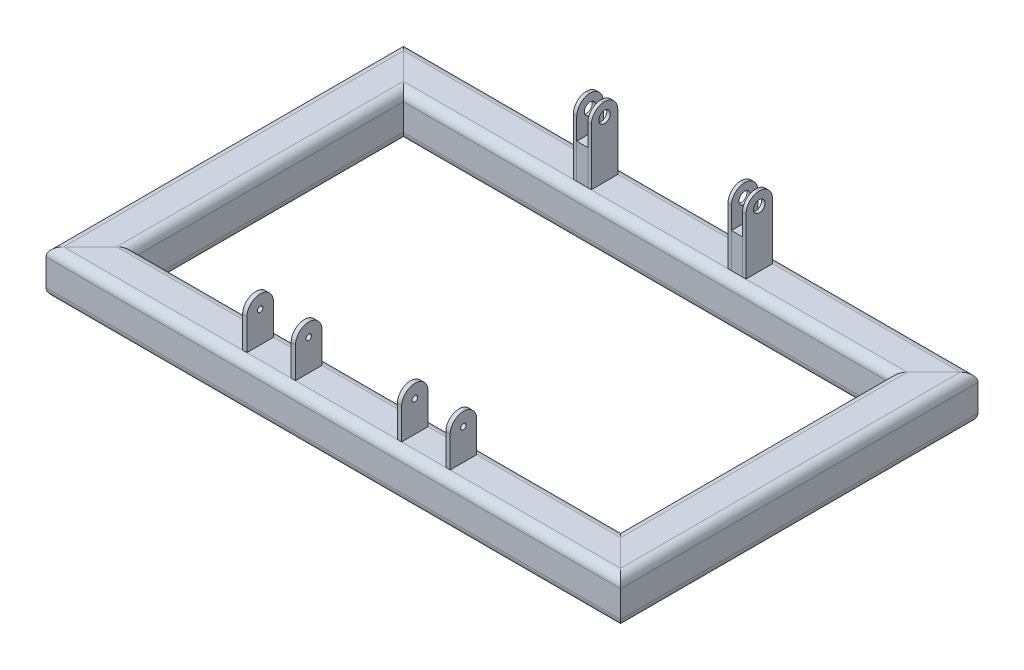
SolidWorks part; units mm, degrees
ref_plane "Front Plane" through (0, 0, 0) normal (0, 0, 1) x (1, 0, 0)
ref_plane "Top Plane" through (0, 0, 0) normal (0, 1, 0) x (1, 0, 0)
ref_plane "Right Plane" through (0, 0, 0) normal (1, 0, 0) x (0, 0, -1)
sketch "Sketch1" plane through (0, 0, 0) normal (0, 1, 0) x (1, 0, 0)
  line L0 (0, 0) -> (0, 180)
  line L5 (0, 180) -> (304.8, 180)
  line L6 (304.8, 180) -> (304.8, 0)
  line L7 (304.8, 0) -> (0, 0)
  dimension "D1" = 180
  dimension "D2" = 304.8
other "Tube square TS25X25X2.5(1)"
ref_plane "Plane1" through (304.8, 0, 0) normal (-1, 0, 0) x (0, 0, 1)
sketch "Sketch123" plane through (304.8, 0, 0) normal (-1, 0, 0) x (0, 0, 1)
  line L0 (-7.62, -10.16) -> (7.62, -10.16)
  line L1 (-10.16, -7.62) -> (-10.16, 7.62)
  line L2 (7.62, 10.16) -> (-7.62, 10.16)
  line L3 (10.16, 7.62) -> (10.16, -7.62)
  line L4 (-7.62, -12.7) -> (7.62, -12.7)
  line L5 (-12.7, -7.62) -> (-12.7, 7.62)
  line L6 (7.62, 12.7) -> (-7.62, 12.7)
  line L7 (12.7, 7.62) -> (12.7, -7.62)
  line L8 (-12.7, 0) -> (-10.16, 0) construction
  line L9 (-10.16, 0) -> (10.16, 0) construction
  line L10 (10.16, 0) -> (12.7, 0) construction
  line L11 (0, 12.7) -> (0, 10.16) construction
  line L12 (0, 10.16) -> (0, -10.16) construction
  line L13 (0, -10.16) -> (0, -12.7) construction
  arc A0 (12.7, 7.62) -> (7.62, 12.7) centre (7.62, 7.62) ccw
  arc A1 (7.62, -12.7) -> (12.7, -7.62) centre (7.62, -7.62) ccw
  arc A2 (-12.7, -7.62) -> (-7.62, -12.7) centre (-7.62, -7.62) ccw
  arc A3 (-7.62, 12.7) -> (-12.7, 7.62) centre (-7.62, 7.62) ccw
  arc A4 (-7.62, 10.16) -> (-10.16, 7.62) centre (-7.62, 7.62) ccw
  arc A5 (10.16, 7.62) -> (7.62, 10.16) centre (7.62, 7.62) ccw
  arc A6 (7.62, -10.16) -> (10.16, -7.62) centre (7.62, -7.62) ccw
  arc A7 (-10.16, -7.62) -> (-7.62, -10.16) centre (-7.62, -7.62) ccw
  point P6 (-12.7, 12.7)
  point P33 (12.7, 12.7)
  point P34 (-12.7, -12.7)
  point P36 (12.7, -12.7)
  point P37 (0, 0)
  point P38 (0, 0)
  dimension "D1" = 5.08
  dimension "Thickness" = 2.54
  dimension "V_leg" = 25.4
  dimension "H_leg" = 25.4
sketch "Sketch124" plane through (0, 12.7, 0) normal (0, 1, 0) x (1, 0, 0)
  line L0 (184.1022, 7.62) -> (184.1022, -7.62)
  line L1 (7.62, 7.62) -> (297.18, 7.62) construction
  line L2 (-7.62, -7.62) -> (312.42, -7.62) construction
  line L3 (123.1022, 7.62) -> (123.1022, -7.62)
  line L4 (186.6022, 7.62) -> (186.6022, -7.62)
  line L5 (125.6022, 7.62) -> (125.6022, -7.62)
  line L6 (123.1022, 7.62) -> (125.6022, 7.62)
  line L7 (125.6022, -7.62) -> (123.1022, -7.62)
  line L8 (184.1022, 7.62) -> (186.6022, 7.62)
  line L9 (186.6022, -7.62) -> (184.1022, -7.62)
  line L10 (97.7022, 7.62) -> (97.7022, -7.62)
  line L11 (97.7022, 7.62) -> (95.2001, 7.62)
  line L12 (95.2001, 7.62) -> (95.2001, -7.62)
  line L13 (95.2001, -7.62) -> (97.7022, -7.62)
  line L15 (214.5022, 7.62) -> (212.0022, 7.62)
  line L16 (214.5022, 7.62) -> (214.5022, -7.62)
  line L17 (214.5022, -7.62) -> (212.0022, -7.62)
  line L18 (212.0022, 7.62) -> (212.0022, -7.62)
  dimension "D1" = 63.5
  dimension "D2" = 2.5
  dimension "D3" = 2.5
  dimension "D4" = 25.4
  dimension "D5" = 25.4
  dimension "D6" = 2.5
extrude "Boss-Extrude1" add sketch "Sketch124" along normal blind 25.4 separate body
sketch "Sketch125" plane through (95.2001, 0, 0) normal (-1, 0, 0) x (0, 0, 1)
  line L0 (-7.62, 38.1) -> (7.62, 22.86)
  line L5 (7.62, 38.1) -> (7.62, 12.7) construction
  line L12 (-9.4911, 42.4789) -> (18.2056, 42.1099)
  line L14 (7.62, 38.1) -> (-7.62, 22.86)
  line L15 (-7.62, 38.1) -> (-7.62, 12.7) construction
  line L16 (-9.4911, 42.4789) -> (-7.62, 30.48)
  line L17 (18.2056, 42.1099) -> (7.62, 30.48)
  arc A2 (-7.62, 30.48) -> (7.62, 30.48) centre (0, 30.48) cw
  circle A3 centre (0, 30.48) radius 1.5875
  dimension "D1" = 3.175
extrude "Cut-Extrude1" cut sketch "Sketch125" against normal through all
sketch "Sketch126" plane through (0, 12.7, 0) normal (0, 1, 0) x (1, 0, 0)
  line L0 (186.6022, 7.62) -> (212.0022, 7.62)
  line L1 (7.62, 7.62) -> (297.18, 7.62) construction
  line L2 (186.6022, -7.62) -> (186.6022, 7.62) construction
  line L3 (199.3022, 7.62) -> (199.3022, 227.2345)
  line L4 (97.7022, 7.62) -> (123.1022, 7.62)
  line L5 (110.4022, 7.62) -> (110.4022, 227.2345)
  line L6 (113.5772, 187.62) -> (113.5772, 172.38)
  line L7 (312.42, 187.62) -> (-7.62, 187.62) construction
  line L8 (297.18, 172.38) -> (7.62, 172.38) construction
  line L9 (107.2272, 187.62) -> (107.2272, 172.38)
  line L10 (107.2272, 187.62) -> (113.5772, 187.62)
  line L11 (107.2272, 172.38) -> (113.5772, 172.38)
  line L12 (196.1222, 187.62) -> (196.1222, 172.38)
  line L14 (196.1222, 172.38) -> (202.4822, 172.38)
  line L15 (202.4822, 172.38) -> (202.4822, 187.62)
  line L16 (202.4822, 187.62) -> (196.1222, 187.62)
  line L18 (196.1222, 187.62) -> (194.1222, 187.62)
  line L19 (196.1222, 187.62) -> (196.1222, 172.38)
  line L20 (196.1222, 172.38) -> (194.1222, 172.38)
  line L21 (194.1222, 187.62) -> (194.1222, 172.38)
  line L22 (202.4822, 187.62) -> (204.4822, 187.62)
  line L23 (202.4822, 187.62) -> (202.4822, 172.38)
  line L24 (202.4822, 172.38) -> (204.4822, 172.38)
  line L25 (204.4822, 187.62) -> (204.4822, 172.38)
  line L26 (107.2272, 187.62) -> (105.2272, 187.62)
  line L27 (107.2272, 187.62) -> (107.2272, 172.38)
  line L28 (107.2272, 172.38) -> (105.2272, 172.38)
  line L29 (105.2272, 187.62) -> (105.2272, 172.38)
  line L30 (113.5772, 187.62) -> (115.5772, 187.62)
  line L31 (113.5772, 187.62) -> (113.5772, 172.38)
  line L32 (113.5772, 172.38) -> (115.5772, 172.38)
  line L33 (115.5772, 187.62) -> (115.5772, 172.38)
  line M12 (7.62, 172.38) -> (297.18, 172.38)
  line M14 (312.42, 187.62) -> (-7.62, 187.62)
  dimension "D1" = 3.175
  dimension "D2" = 6.35
  dimension "D3" = 3.18
  dimension "D4" = 3.18
  dimension "D5" = 2
  dimension "D6" = 2
  dimension "D7" = 2
  dimension "D8" = 2
extrude "Boss-Extrude2" add sketch "Sketch126" along normal blind 40 separate body contours L33 L6 M14 M12 | L29 L9 M14 M12 | L25 L15 M14 M12 | L21 L12 M14 M12
sketch "Sketch129" plane through (204.4822, 0, 0) normal (1, 0, 0) x (0, 0, -1)
  line L1 (187.62, 52.7) -> (187.62, 12.7) construction
  line L3 (172.38, 52.7) -> (172.38, 12.7) construction
  line L5 (172.38, 45.1101) -> (170.0365, 54.6654)
  line L6 (170.0365, 54.6654) -> (189.9348, 53.926)
  line L7 (189.9348, 53.926) -> (187.62, 45.1101)
  arc A0 (172.38, 45.1101) -> (187.62, 45.1101) centre (180, 45.0959) cw
  circle A1 centre (180, 45.0959) radius 3.295
  point P1 (180, 45.1101)
  dimension "D1" = 6.59
extrude "Cut-Extrude7" cut sketch "Sketch129" against normal through all
sketch "Sketch130" plane through (0, 12.7, 0) normal (0, 1, 0) x (1, 0, 0)
  line L1 (107.2272, 187.62) -> (113.5772, 187.62)
  line L2 (107.2272, 187.62) -> (107.2272, 172.38)
  line L3 (107.2272, 172.38) -> (113.5772, 172.38)
  line L4 (113.5772, 187.62) -> (113.5772, 172.38)
  line L5 (196.1222, 187.62) -> (202.4822, 187.62)
  line L6 (196.1222, 187.62) -> (196.1222, 172.38)
  line L7 (196.1222, 172.38) -> (202.4822, 172.38)
  line L8 (202.4822, 187.62) -> (202.4822, 172.38)
extrude "Boss-Extrude3" add sketch "Sketch130" along normal blind 20 separate body
